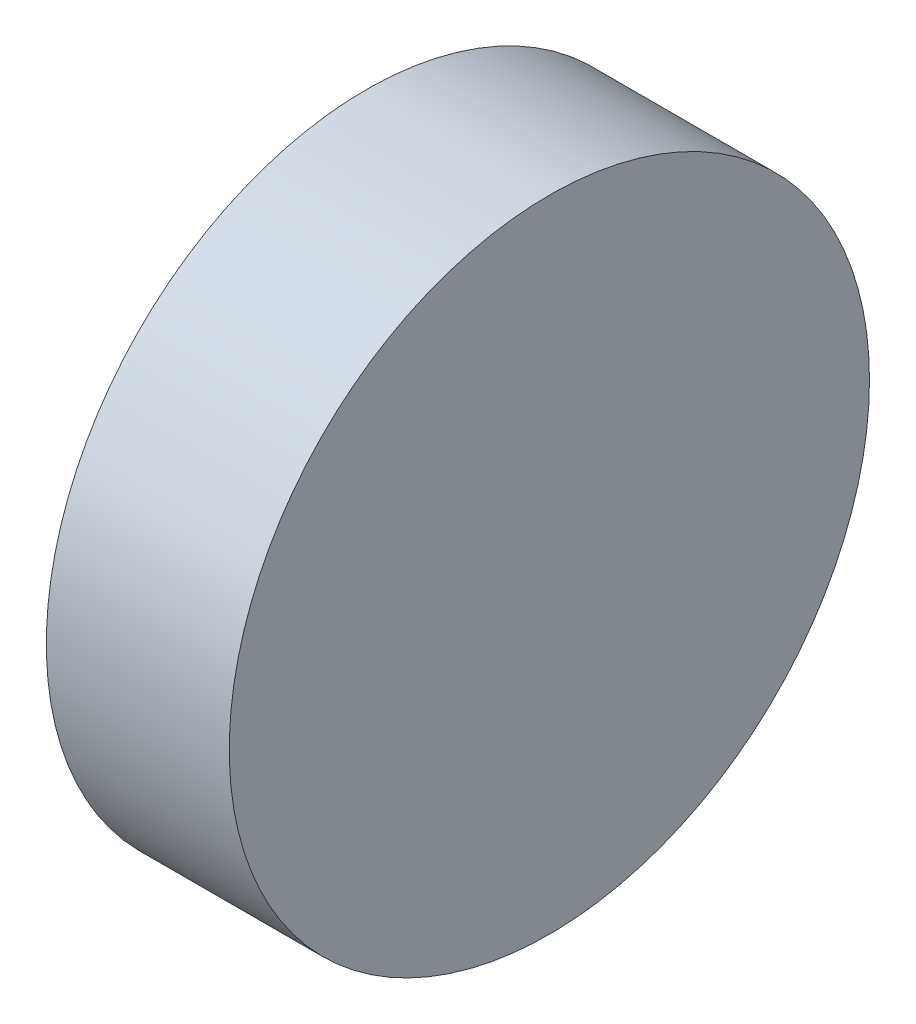
SolidWorks part; units mm, degrees
ref_plane "Front Plane" through (0, 0, 0) normal (0, 0, 1) x (1, 0, 0)
ref_plane "Top Plane" through (0, 0, 0) normal (0, 1, 0) x (1, 0, 0)
ref_plane "Right Plane" through (0, 0, 0) normal (1, 0, 0) x (0, 0, -1)
sketch "Sketch1" plane through (0, 0, 0) normal (1, 0, 0) x (0, 0, -1)
  circle A0 centre (0, 0) radius 1.75
  circle A2 centre (0, 0) radius 1.75 construction
extrude "Boss-Extrude1" add sketch "Sketch1" along normal blind 1
